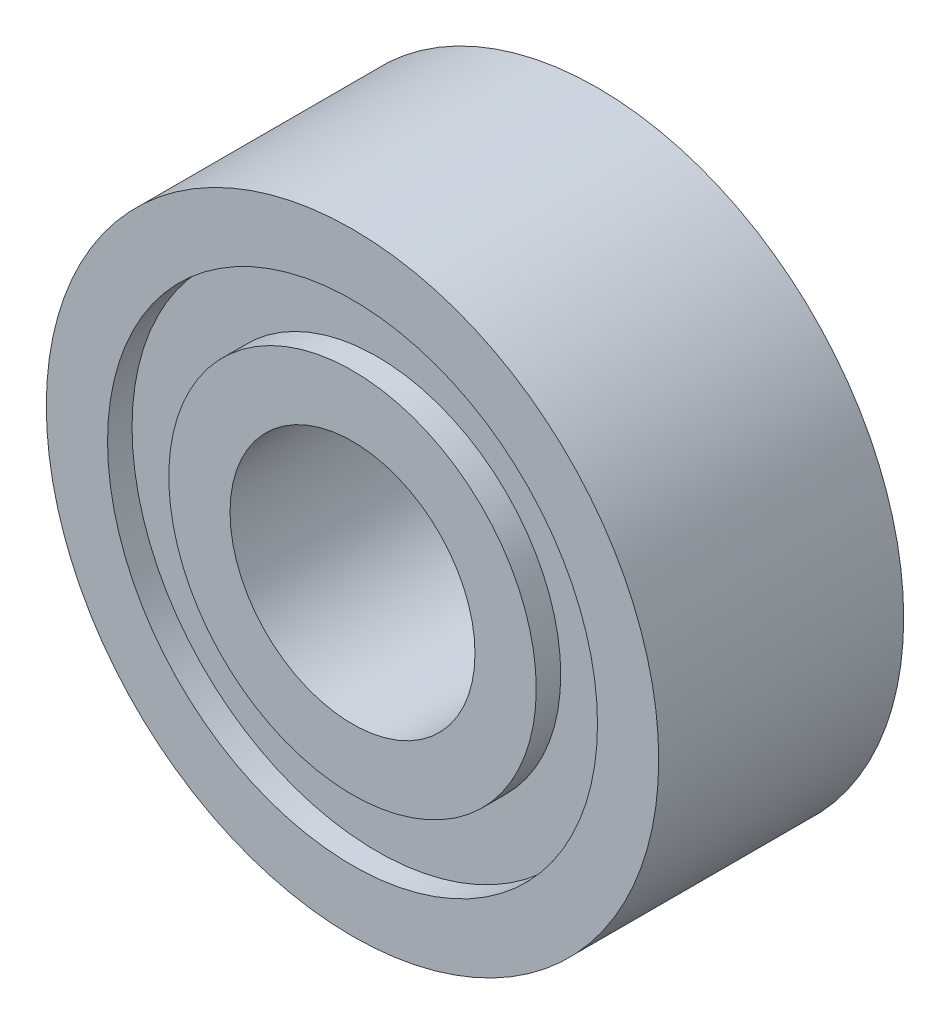
SolidWorks part; units mm, degrees
ref_plane "Front Plane" through (0, 0, 0) normal (0, 0, 1) x (1, 0, 0)
ref_plane "Top Plane" through (0, 0, 0) normal (0, 1, 0) x (1, 0, 0)
ref_plane "Right Plane" through (0, 0, 0) normal (1, 0, 0) x (0, 0, -1)
sketch "Sketch2" plane through (0, 0, 0) normal (1, 0, 0) x (0, 0, -1)
  line L0 (0, 0) -> (4.251, 0) construction
  line L1 (1.1092, 2.5) -> (3.1092, 2.5)
  line L2 (3.1092, 2.5) -> (3.1092, 2)
  line L3 (3.1092, 2) -> (2.9092, 2)
  line L4 (2.9092, 2) -> (2.9092, 1.5)
  line L5 (2.9092, 1.5) -> (3.1092, 1.5)
  line L6 (3.1092, 1.5) -> (3.1092, 1)
  line L7 (3.1092, 1) -> (1.1092, 1)
  line L8 (1.1092, 1) -> (1.1092, 1.5)
  line L9 (1.1092, 1.5) -> (1.3092, 1.5)
  line L10 (1.3092, 1.5) -> (1.3092, 2)
  line L11 (1.3092, 2) -> (1.1092, 2)
  line L12 (1.1092, 2) -> (1.1092, 2.5)
  point P14 (2.1092, 2.5)
  point P16 (2.1092, 1)
  dimension "D1" = 2
  dimension "D2" = 2
  dimension "D3" = 5
  dimension "D4" = 0.5
  dimension "D5" = 0.2
  dimension "D6" = 0.5
revolve "Revolve1" add sketch "Sketch2" angle 360 about L0
